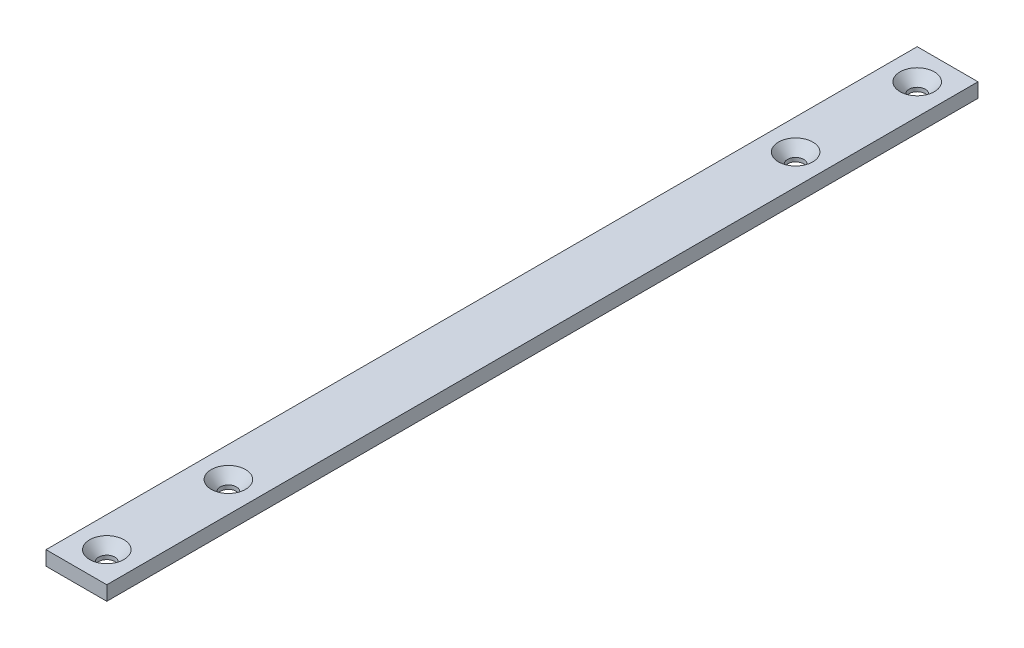
SolidWorks part; units mm, degrees
ref_plane "Front Plane" through (0, 0, 0) normal (0, 0, 1) x (1, 0, 0)
ref_plane "Top Plane" through (0, 0, 0) normal (0, 1, 0) x (1, 0, 0)
ref_plane "Right Plane" through (0, 0, 0) normal (1, 0, 0) x (0, 0, -1)
sketch "Sketch1" plane through (0, 0, 0) normal (0, 0, 1) x (1, 0, 0)
  line L0 (0, 3.9688) -> (0, -3.9688)
  line L1 (-12.7, 0) -> (12.7, 0) construction
  point P6 (0, 0)
  dimension "Width" = 25.4
  dimension "Thk" = 7.9375
sketch "Sketch2" plane through (0, 0, 0) normal (1, 0, 0) x (0, 0, -1)
  line L0 (152.4, 0) -> (-152.4, 0)
  point P4 (0, 0)
  dimension "Length" = 304.8
sketch "Sketch3" plane through (0, 0, 0) normal (0, 0, 1) x (1, 0, 0)
  line L5 (12.7, -3) -> (-12.7, -3)
  line L6 (12.7, -3) -> (12.7, 3)
  line L7 (12.7, 3) -> (-12.7, 3)
  line L8 (-12.7, -3) -> (-12.7, 3)
  line L9 (12.7, -3) -> (-12.7, 3) construction
  line L10 (12.7, 3) -> (-12.7, -3) construction
  point P0 (0, 0)
  point P1 (0, 0)
  dimension "D1" = 25.4
  dimension "D2" = 6
extrude "Boss-Extrude1" add sketch "Sketch3" along normal mid plane 364
sketch "Sketch5" plane through (0, 3, 0) normal (0, 1, 0) x (1, 0, 0)
  line L2 (12.7, 0) -> (-12.7, 0) construction
  line L3 (12.7, -182) -> (12.7, 182) construction
  line L4 (12.7, 182) -> (-12.7, 182) construction
  circle A0 centre (0, 169.3) radius 3.5
  circle A1 centre (0, -169.3) radius 3.5
  circle A2 centre (0, 118.5) radius 3.5
  circle A3 centre (0, -118.5) radius 3.5
  dimension "D1" = 7
  dimension "D2" = 12.7
  dimension "D3" = 12.7
  dimension "D4" = 7
  dimension "D5" = 50.8
hole_wizard "CSK for 1/4 Flat Head Socket Cap Screw1" positions "Sketch7" profile "Sketch8" countersink size "1/4" standard "ANSI Inch" end condition through all
sketch "Sketch7" plane through (0, 3, 0) normal (0, 1, 0) x (1, 0, 0)
  point P0 (0, 169.3)
  point P3 (0, -169.3)
  point P6 (0, 118.5)
  point P9 (0, -118.5)
sketch "Sketch8" plane through (0, 3, -169.3) normal (1, 0, 0) x (0, 0, 1)
  line L0 (0, 0) -> (0, 6)
  line L1 (0, 6) -> (3.3782, 6)
  line L2 (3.3782, 6) -> (3.3782, 4.3716)
  line L3 (3.3782, 4.3716) -> (7.1783, 0)
  line L5 (7.1783, 0) -> (0, 0)
  line L6 (-3.3782, 4.3716) -> (-7.1783, 0) construction
  line L11 (0, -6.35) -> (0, 107.95) construction
  dimension "Thru Hole Dia." = 6.7564
  dimension "Thru Hole Depth" = 6
  dimension "Near C'Sink Dia." = 14.3567
  dimension "Near C'Sink Angle" = 82
